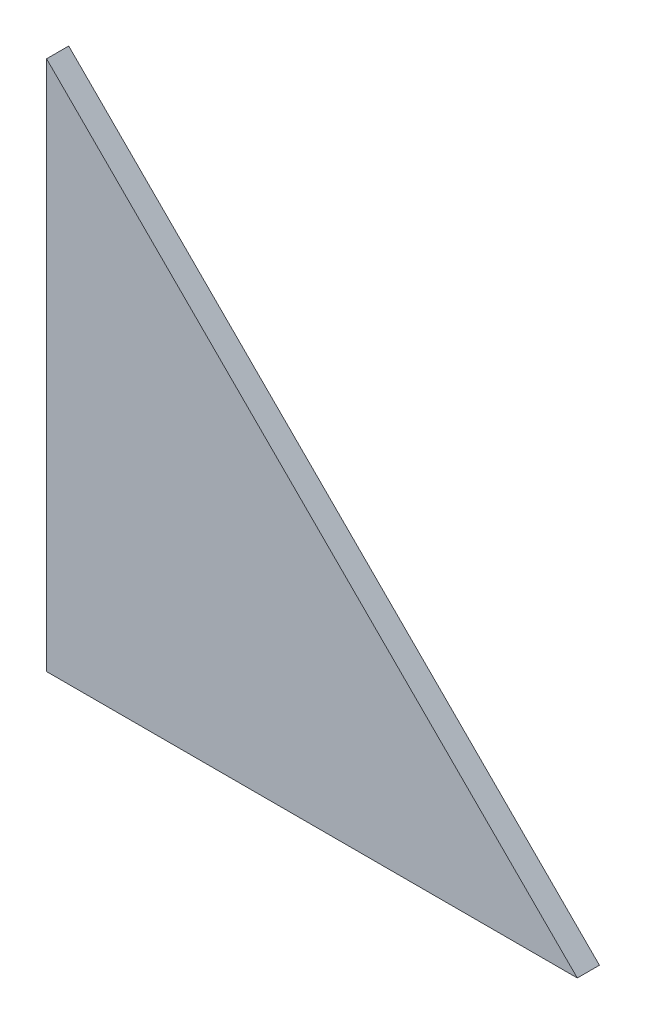
SolidWorks part; units mm, degrees
ref_plane "Front Plane" through (0, 0, 0) normal (0, 0, 1) x (1, 0, 0)
ref_plane "Top Plane" through (0, 0, 0) normal (0, 1, 0) x (1, 0, 0)
ref_plane "Right Plane" through (0, 0, 0) normal (1, 0, 0) x (0, 0, -1)
sketch "Sketch1" plane through (0, 0, 0) normal (0, 0, 1) x (1, 0, 0)
  line L0 (0, 0) -> (0, 120)
  line L1 (0, 0) -> (120, 0)
  line L2 (120, 0) -> (0, 120)
  dimension "D1" = 120
  dimension "D2" = 120
extrude "Boss-Extrude1" add sketch "Sketch1" along normal blind 5 contours L2 L0 L1
